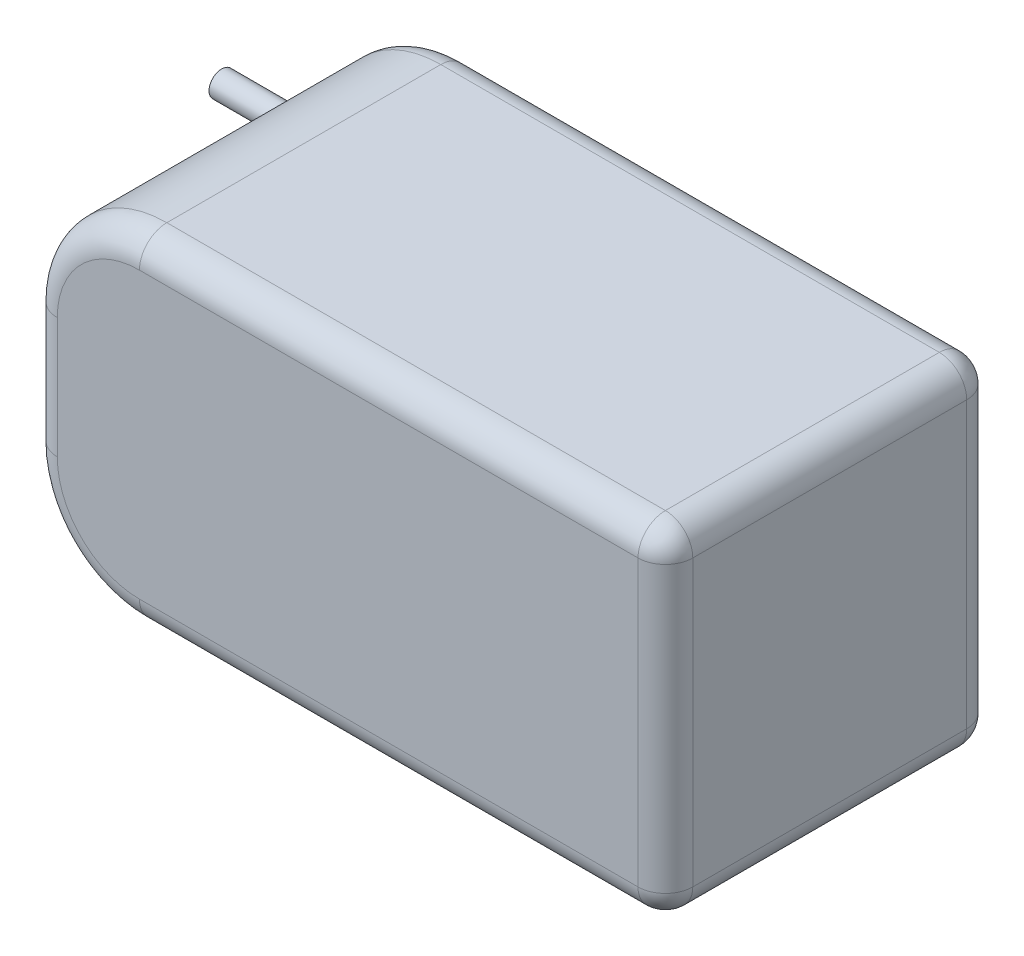
SolidWorks part; units mm, degrees
ref_plane "Front Plane" through (0, 0, 0) normal (0, 0, 1) x (1, 0, 0)
ref_plane "Top Plane" through (0, 0, 0) normal (0, 1, 0) x (1, 0, 0)
ref_plane "Right Plane" through (0, 0, 0) normal (1, 0, 0) x (0, 0, -1)
sketch "Sketch1" plane through (0, 0, 0) normal (0, 1, 0) x (1, 0, 0)
  line L1 (-29, 15) -> (29, 15)
  line L2 (-29, 15) -> (-29, -15)
  line L3 (-29, -15) -> (29, -15)
  line L4 (29, 15) -> (29, -15)
  line L5 (-29, 15) -> (29, -15) construction
  line L6 (-29, -15) -> (29, 15) construction
  point P0 (0, 0)
  dimension "D1" = 58
  dimension "D2" = 30
extrude "Boss-Extrude1" add sketch "Sketch1" along normal blind 31
fillet "Fillet1" radius 10 2 edges at (-29, 0, 0) (-29, 31, 0)
fillet "Fillet2" radius 2.5 14 edges at (5, 0, 15) (-26.0711, 2.9289, 15) (-29, 15.5, 15) (-26.0711, 28.0711, 15) (5, 0, -15) (-26.0711, 2.9289, -15) (-29, 15.5, -15) (-26.0711, 28.0711, -15) (29, 31, 0) (5, 31, 15) (5, 31, -15) (29, 15.5, 15) (29, 15.5, -15) (29, 0, 0)
sketch "Sketch2" plane through (-29, 0, 0) normal (-1, 0, 0) x (0, 0, 1)
  line L0 (-12.5, 21) -> (-12.5, 10) construction
  line L1 (-15, 15.5) -> (15, 15.5) construction
  line L2 (-15, 10) -> (-15, 21) construction
  line L3 (15, 21) -> (15, 10) construction
  circle A0 centre (-12.5, 19.5) radius 1.15
  circle A1 centre (-12.5, 11.5) radius 1.15
  dimension "D1" = 2.3
  dimension "D2" = 8
extrude "Boss-Extrude2" add sketch "Sketch2" along normal blind 10
